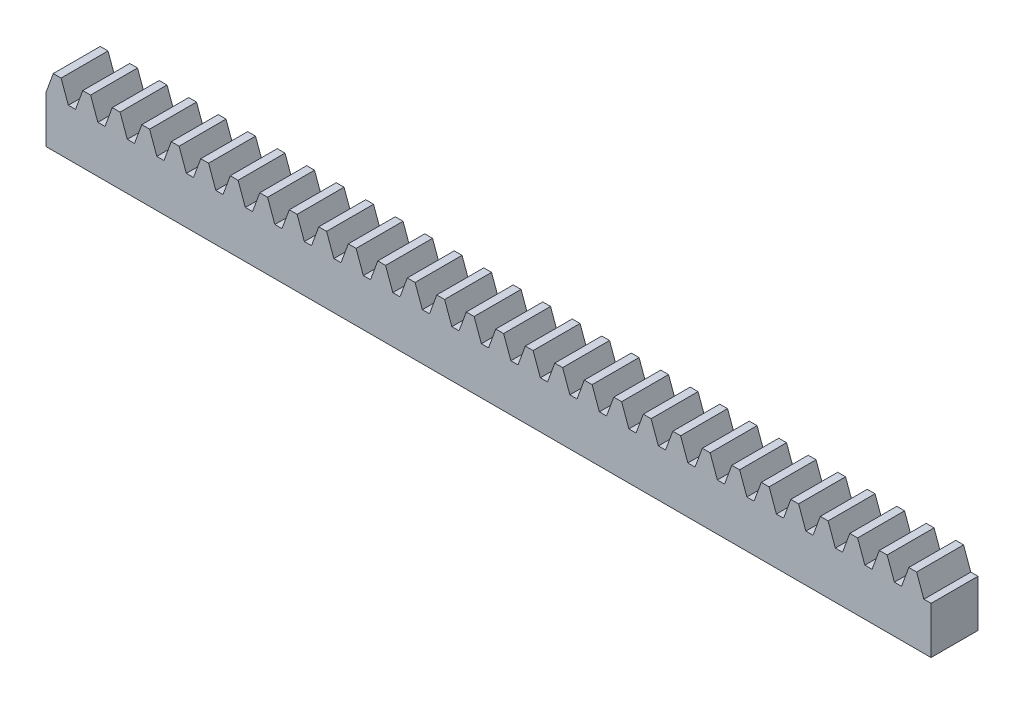
SolidWorks part; units mm, degrees
ref_plane "Plan de face" through (0, 0, 0) normal (0, 0, 1) x (1, 0, 0)
ref_plane "Plan de dessus" through (0, 0, 0) normal (0, 1, 0) x (1, 0, 0)
ref_plane "Plan de droite" through (0, 0, 0) normal (1, 0, 0) x (0, 0, -1)
sketch "Esquisse1" plane through (0, 0, 0) normal (0, 0, 1) x (1, 0, 0)
  line L0 (0, 2.1718) -> (0, 0) construction
  line L1 (-4.5073, 0) -> (3.439, 0) construction
  line L3 (0, 0) -> (3.0665, 1.1161) construction
  line L5 (0.8311, 2) -> (2.378, -2.25)
  line L7 (-0.8311, 2) -> (-2.378, -2.25)
  line L8 (-0.8311, 2) -> (0.8311, 2)
  line L9 (-2.378, -2.25) -> (3.905, -2.25) construction
  line L10 (2.378, -2.25) -> (3.905, -2.25)
  line L11 (-2.378, -2.25) -> (-2.378, -12.25)
  line L12 (3.905, -2.25) -> (3.905, -12.25)
  line L13 (3.905, -12.25) -> (-2.378, -12.25)
  circle A0 centre (0, 0) radius 1.615 construction
  circle A1 centre (0, 0) radius 1.465 construction
  dimension "D1" = 0.15
  dimension "D2" = 3.23
  dimension "D3" = 20
  dimension "D4" = 2
  dimension "D5" = 2.25
  dimension "D6" = 6.283
  dimension "D7" = 10
extrude "Boss.-Extru.1" add sketch "Esquisse1" along normal blind 10
pattern_linear "Répétition linéaire1" count 30 spacing 6.283 along (1, 0, 0) of "Boss.-Extru.1"
